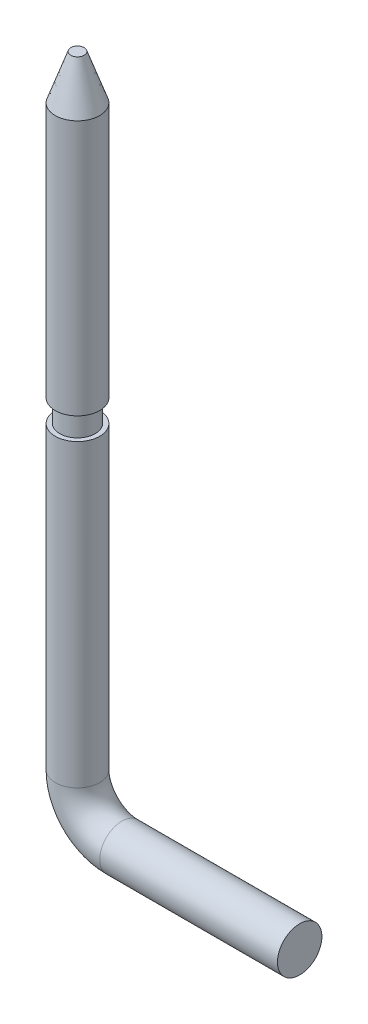
SolidWorks part; units mm, degrees
ref_plane "Front Plane" through (0, 0, 0) normal (0, 0, 1) x (1, 0, 0)
ref_plane "Top Plane" through (0, 0, 0) normal (0, 1, 0) x (1, 0, 0)
ref_plane "Right Plane" through (0, 0, 0) normal (1, 0, 0) x (0, 0, -1)
sketch "Sketch1" plane through (0, 0, 0) normal (0, 0, 1) x (1, 0, 0)
  line L0 (0, 30) -> (0, 2)
  line L1 (2, 0) -> (10, 0)
  arc A0 (0, 2) -> (2, 0) centre (2, 2) ccw
  point P6 (0, 0)
  dimension "D3" = 2
  dimension "D1" = 30
  dimension "D2" = 10
ref_plane "Plane1" through (10, 0, 0) normal (1, 0, 0) x (0, 0, -1)
sketch "Sketch2" plane through (10, 0, 0) normal (1, 0, 0) x (0, 0, -1)
  circle A0 centre (0, 0) radius 1
  dimension "D1" = 2
sweep "Sweep1" add profiles "Sketch2" path "Sketch1"
sketch "Sketch3" plane through (0, 0, 0) normal (0, 0, 1) x (1, 0, 0)
  line L0 (-0.3, 30) -> (-1, 28)
  line L1 (1, 30) -> (-1, 30) construction
  line L2 (-1, 30) -> (-1, 2) construction
  line L3 (-1, 28) -> (-1, 30)
  line L4 (-1, 30) -> (-0.3, 30)
  line L5 (0, 30) -> (0, 0) construction
  line L6 (1, 16) -> (-0.8, 16) construction
  line L7 (-1, 16.5) -> (-0.8, 16.5)
  line L8 (-1, 16.5) -> (-1, 15.5)
  line L9 (-1, 15.5) -> (-0.8, 15.5)
  line L10 (-0.8, 16.5) -> (-0.8, 15.5)
  line L11 (1, 2) -> (1, 30) construction
  dimension "D1" = 0.7
  dimension "D2" = 2
  dimension "D3" = 1
  dimension "D4" = 0.2
revolve "Cut-Revolve1" cut sketch "Sketch3" angle 360 about L5
